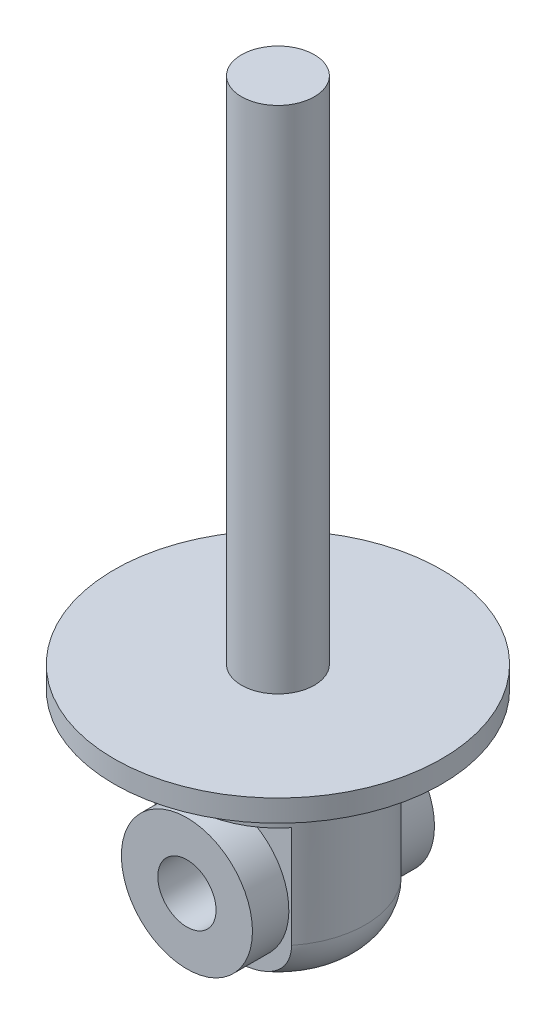
SolidWorks part; units mm, degrees
ref_plane "Płaszczyzna przednia" through (0, 0, 0) normal (0, 0, 1) x (1, 0, 0)
ref_plane "Płaszczyzna górna" through (0, 0, 0) normal (0, 1, 0) x (1, 0, 0)
ref_plane "Płaszczyzna prawa" through (0, 0, 0) normal (1, 0, 0) x (0, 0, -1)
sketch "Sketch1" plane through (0, 0, 0) normal (0, 1, 0) x (1, 0, 0)
  circle A0 centre (0, 0) radius 22.5
  dimension "D1" = 45
extrude "Boss-Extrude1" add sketch "Sketch1" along normal blind 3
sketch "Sketch2" plane through (0, 3, 0) normal (0, 1, 0) x (1, 0, 0)
  circle A0 centre (0, 0) radius 5
  dimension "D1" = 10
extrude "Boss-Extrude2" add sketch "Sketch2" along normal blind 70
sketch "Sketch3" plane through (0, 0, 0) normal (0, -1, 0) x (1, 0, 0)
  circle A0 centre (0, 0) radius 12
  dimension "D1" = 24
extrude "Boss-Extrude3" add sketch "Sketch3" along normal blind 28
fillet "Fillet1" radius 6 1 edges at (0, -28, -12)
sketch "Sketch4" plane through (0, 0, 0) normal (1, 0, 0) x (0, 0, -1)
  line L0 (0, 0) -> (0, -28) construction
  line L10 (-12, 0) -> (12, 0) construction
  line L11 (-6, -28) -> (6, -28) construction
  line L12 (7.5, -28) -> (21.41, -28)
  line L13 (21.41, -28) -> (21.41, -8)
  line L14 (21.41, -8) -> (7.5, -8)
  line L15 (7.5, -8) -> (7.5, -28)
  line L16 (-7.5, -8) -> (-7.5, -28)
  line L17 (-21.41, -8) -> (-7.5, -8)
  line L18 (-21.41, -28) -> (-21.41, -8)
  line L19 (-7.5, -28) -> (-21.41, -28)
  dimension "D1" = 15
  dimension "D2" = 20
extrude "Cut-Extrude1" cut sketch "Sketch4" against normal through all both and the other way through all
sketch "Sketch8" plane through (0, 0, -7.5) normal (0, 0, -1) x (-1, 0, 0)
  line L0 (0, 0) -> (0, -28) construction
  line L1 (-6, -28) -> (6, -28) construction
  circle A0 centre (0, -18) radius 4
  dimension "D2" = 8
  dimension "D1" = 10
extrude "Cut-Extrude3" cut sketch "Sketch8" against normal through all
sketch "Sketch10" plane through (0, 0, 0) normal (0, 0, 1) x (1, 0, 0)
  circle A0 centre (0, -18) radius 9
  circle A1 centre (0, -18) radius 4 construction
  circle A2 centre (0, -18) radius 4
  dimension "D1" = 18
extrude "Boss-Extrude5" add sketch "Sketch10" along normal mid plane 25
